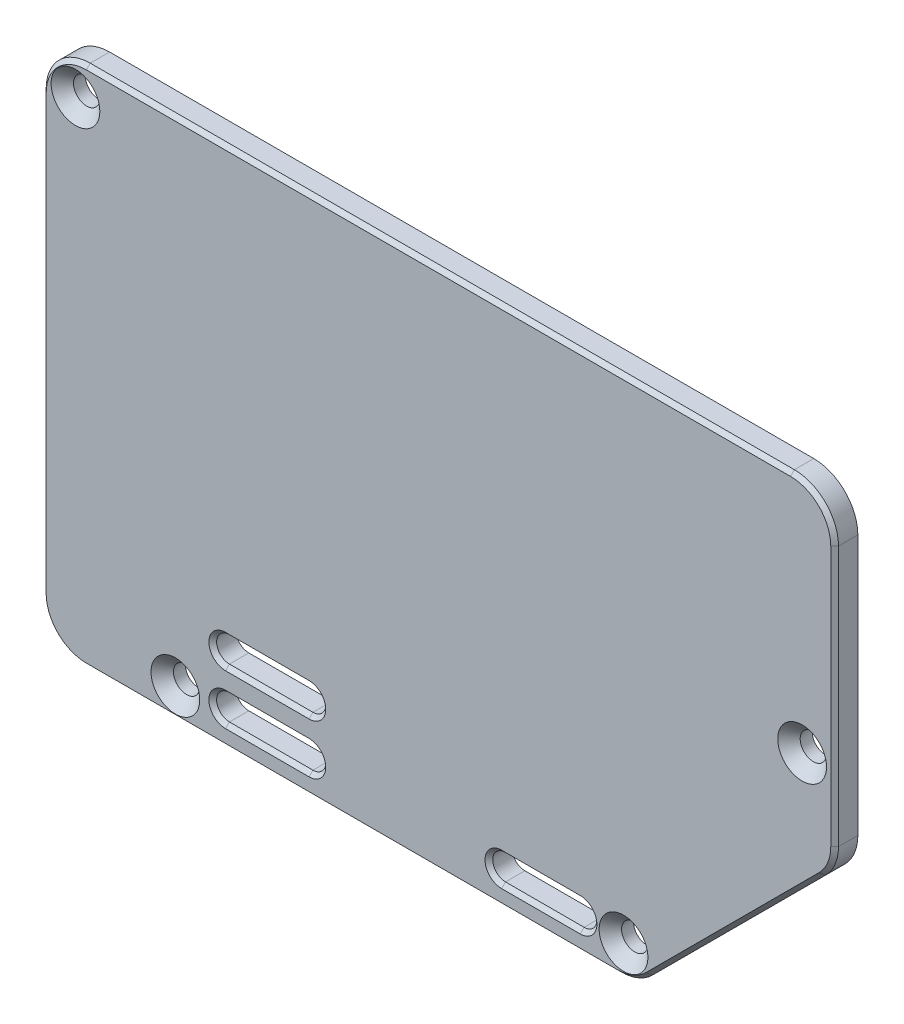
SolidWorks part; units mm, degrees
ref_plane "Front Plane" through (0, 0, 0) normal (0, 0, 1) x (1, 0, 0)
ref_plane "Top Plane" through (0, 0, 0) normal (0, 1, 0) x (1, 0, 0)
ref_plane "Right Plane" through (0, 0, 0) normal (1, 0, 0) x (0, 0, -1)
sketch "Sketch2" plane through (0, 0, 8.62) normal (0, 0, 1) x (1, 0, 0)
  line L0 (4.5, 66.2) -> (95.5, 66.2)
  line L1 (101.2, 60.5) -> (101.2, 26.864)
  line L2 (99.5305, 22.8335) -> (77.1665, 0.4695)
  line L3 (73.136, -1.2) -> (4.5, -1.2)
  line L4 (-1.2, 4.5) -> (-1.2, 60.5)
  line L5 (-1.5, 60.5) -> (-1.5, 4.5) construction
  arc A0 (4.5, -1.2) -> (-1.2, 4.5) centre (4.5, 4.5) cw
  arc A1 (77.1665, 0.4695) -> (73.136, -1.2) centre (73.136, 4.5) cw
  arc A2 (101.2, 26.864) -> (99.5305, 22.8335) centre (95.5, 26.864) cw
  arc A3 (95.5, 66.2) -> (101.2, 60.5) centre (95.5, 60.5) cw
  arc A4 (4.5, 66.2) -> (-1.2, 60.5) centre (4.5, 60.5) ccw
  arc A5 (-1.5, 4.5) -> (4.5, -1.5) centre (4.5, 4.5) ccw construction
  arc A6 (4.5, 66.5) -> (-1.5, 60.5) centre (4.5, 60.5) ccw construction
  arc A7 (101.5, 60.5) -> (95.5, 66.5) centre (95.5, 60.5) ccw construction
  arc A8 (73.136, -1.5) -> (77.3787, 0.2574) centre (73.136, 4.5) ccw construction
  circle A9 centre (3.0858, 61.9142) radius 1.5 construction
  circle A10 centre (16, 2.5) radius 1.5 construction
  circle A11 centre (73.9175, 2.659) radius 1.5 construction
  circle A12 centre (97, 35.5) radius 1.5 construction
  arc A14 (101.3205, 25.4074) -> (101.5, 26.864) centre (95.5, 26.864) ccw construction
  dimension "D1" = 0.3
  dimension "D2" = 3
extrude "Boss-Extrude1" add sketch "Sketch2" along normal blind 3
hole_wizard "CSK for M3 Flat Head Machine Screw1" positions "Sketch4" profile "Sketch5" countersink size "M3" standard "ANSI Metric" end condition through all
sketch "Sketch4" plane through (0, 0, 11.62) normal (0, 0, 1) x (1, 0, 0)
  point P0 (3.0858, 61.9142)
  point P3 (16, 2.5)
  point P6 (73.9175, 2.659)
  point P9 (97, 35.5)
sketch "Sketch5" plane through (3.0858, 61.9142, 11.62) normal (1, 0, 0) x (0, -1, 0)
  line L0 (0, 0) -> (0, 3)
  line L1 (0, 3) -> (1.7, 3)
  line L2 (1.7, 3) -> (1.7, 1.45)
  line L3 (1.7, 1.45) -> (3.15, 0)
  line L5 (3.15, 0) -> (0, 0)
  line L6 (-1.7, 1.45) -> (-3.15, 0) construction
  line L11 (0, -6.35) -> (0, 107.95) construction
  dimension "Thru Hole Dia." = 3.4
  dimension "Thru Hole Depth" = 3
  dimension "Near C'Sink Dia." = 6.3
  dimension "Near C'Sink Angle" = 90
sketch "Sketch6" plane through (0, 0, 11.62) normal (0, 0, 1) x (1, 0, 0)
  line L0 (33.278, 9.5885) -> (22.483, 9.5885) construction
  line L1 (33.278, 7.9375) -> (22.483, 7.9375)
  line L2 (33.278, 11.2395) -> (22.483, 11.2395)
  line L3 (33.278, 3.1115) -> (22.483, 3.1115) construction
  line L4 (33.278, 1.4605) -> (22.483, 1.4605)
  line L5 (33.278, 4.7625) -> (22.483, 4.7625)
  line L6 (27.8805, 11.85) -> (27.8805, 9.5885) construction
  line L8 (34.3805, 11.85) -> (21.3805, 11.85) construction
  line L10 (68.326, 3.048) -> (58.166, 3.048) construction
  line L11 (68.326, 1.397) -> (58.166, 1.397)
  line L12 (68.326, 4.699) -> (58.166, 4.699)
  line L13 (27.8805, 3.1115) -> (27.8805, 0.85) construction
  line L14 (21.3805, 0.85) -> (34.3805, 0.85) construction
  arc A0 (33.278, 7.9375) -> (33.278, 11.2395) centre (33.278, 9.5885) ccw
  arc A1 (22.483, 11.2395) -> (22.483, 7.9375) centre (22.483, 9.5885) ccw
  arc A2 (33.278, 1.4605) -> (33.278, 4.7625) centre (33.278, 3.1115) ccw
  arc A3 (22.483, 4.7625) -> (22.483, 1.4605) centre (22.483, 3.1115) ccw
  arc A4 (68.326, 1.397) -> (68.326, 4.699) centre (68.326, 3.048) ccw
  arc A5 (58.166, 4.699) -> (58.166, 1.397) centre (58.166, 3.048) ccw
  point P2 (27.8805, 9.5885)
  point P7 (27.8805, 3.1115)
  point P26 (63.246, 3.048)
  dimension "D1" = 3.302
  dimension "D2" = 3.175
  dimension "D3" = 10.795
  dimension "D4" = 3.302
extrude "Cut-Extrude1" cut sketch "Sketch6" against normal through all
sketch "Sketch7" plane through (0, 0, 11.62) normal (0, 0, 1) x (1, 0, 0)
  line L1 (21.9613, 45.2085) -> (69.9613, 45.2085)
  line L2 (21.3263, 44.5735) -> (21.3263, 8.1735)
  line L3 (21.9613, 7.5385) -> (69.9613, 7.5385)
  line L4 (70.5963, 44.5735) -> (70.5963, 8.1735)
  arc A4 (69.9613, 45.2085) -> (70.5963, 44.5735) centre (69.9613, 44.5735) cw
  arc A5 (69.9613, 7.5385) -> (70.5963, 8.1735) centre (69.9613, 8.1735) ccw
  arc A6 (21.3263, 8.1735) -> (21.9613, 7.5385) centre (21.9613, 8.1735) ccw
  arc A7 (21.9613, 45.2085) -> (21.3263, 44.5735) centre (21.9613, 44.5735) ccw
  dimension "D2" = 0.635
split line "Split Line1" [suppressed]
chamfer "Chamfer1" distance 0.5 angle 45 22 edges at (63.246, 1.397, 11.62) (69.977, 3.048, 11.62) (56.515, 3.048, 11.62) (63.246, 4.699, 11.62) (27.8805, 1.4605, 11.62) (34.929, 3.1115, 11.62) (20.832, 3.1115, 11.62) (27.8805, 4.7625, 11.62) (27.8805, 7.9375, 11.62) (34.929, 9.5885, 11.62) (20.832, 9.5885, 11.62) (27.8805, 11.2395, 11.62) (100.7661, 24.6827, 11.62) (101.2, 43.682, 11.62) (88.3485, 11.6515, 11.62) (99.5305, 64.5305, 11.62) (75.3173, -0.7661, 11.62) (50, 66.2, 11.62) (38.818, -1.2, 11.62) (0.4695, 64.5305, 11.62) (0.4695, 0.4695, 11.62) (-1.2, 32.5, 11.62)
